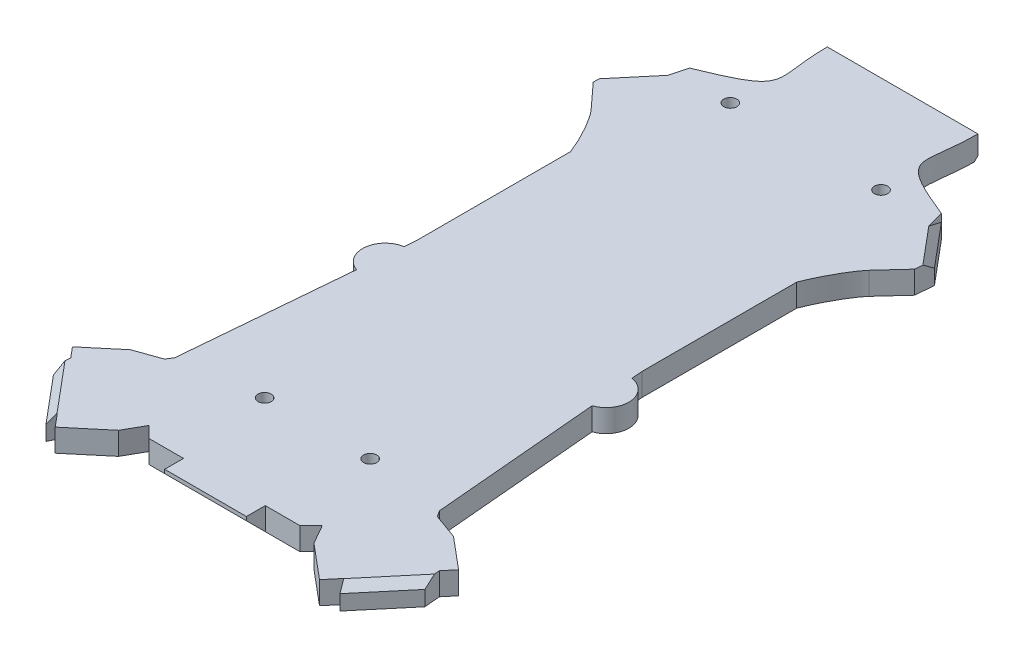
SolidWorks part; units mm, degrees
ref_plane "Front Plane" through (0, 0, 0) normal (0, 0, 1) x (1, 0, 0)
ref_plane "Top Plane" through (0, 0, 0) normal (0, 1, 0) x (1, 0, 0)
ref_plane "Right Plane" through (0, 0, 0) normal (1, 0, 0) x (0, 0, -1)
sketch "Sketch1" plane through (0, 0, 0) normal (0, 1, 0) x (1, 0, 0)
  line L1 (30, -90) -> (-30, -90)
  line L2 (30, -90) -> (30, 90)
  line L3 (30, 90) -> (-30, 90)
  line L4 (-30, -90) -> (-30, 90)
  line L5 (30, -90) -> (-30, 90) construction
  line L6 (30, 90) -> (-30, -90) construction
  point P0 (0, 0)
  dimension "D1" = 60
  dimension "D2" = 180
extrude "Boss-Extrude1" add sketch "Sketch1" along normal blind 6
sketch "Sketch2" plane through (0, 6, 0) normal (0, 1, 0) x (1, 0, 0)
  line L0 (0, -90) -> (0, -59.8277)
  line L1 (-30, -90) -> (30, -90) construction
sketch "Sketch3" plane through (0, 6, 0) normal (0, 1, 0) x (1, 0, 0)
  line L0 (-30, -90) -> (30, -90) construction
  line L1 (15.25, -33.25) -> (-15.25, -33.25)
  line L2 (15.25, -33.25) -> (15.25, -2.75)
  line L3 (15.25, -2.75) -> (-15.25, -2.75)
  line L4 (-15.25, -33.25) -> (-15.25, -2.75)
  line L5 (15.25, -33.25) -> (-15.25, -2.75) construction
  line L6 (15.25, -2.75) -> (-15.25, -33.25) construction
  line L7 (0, -18) -> (0, -90) construction
  point P0 (0, -18)
  dimension "D1" = 30.5
  dimension "D2" = 72
chamfer "Chamfer2" distance 10 angle 45 4 edges at (30, 3, -90) (-30, 3, -90) (-30, 3, 90) (30, 3, 90)
sketch "Sketch52" plane through (0, 6, 0) normal (0, 1, 0) x (1, 0, 0)
  line L0 (0, 28.8816) -> (0, 18.7178) construction
  line L1 (13.2149, 49.8944) -> (24.7851, 36.1056) construction
  line L2 (19, 43) -> (9.9357, 35.3941) construction
  line L4 (30, -80) -> (30, 80) construction
  line L7 (45, 53.0679) -> (36.85, 44.1738)
  line L8 (36.85, 44.1738) -> (30, 25.3535)
  line L10 (30, 79.657) -> (30, 25.3535)
  line L16 (33.4298, 66.8567) -> (45, 53.0679)
  line L17 (-33.4298, 66.8567) -> (-45, 53.0679)
  line L18 (-30, 79.657) -> (-33.4298, 66.8567)
  line L19 (-30, 79.657) -> (-30, 25.3535)
  line L20 (-36.85, 44.1738) -> (-30, 25.3535)
  line L21 (-45, 53.0679) -> (-36.85, 44.1738)
  line L22 (33.4298, 66.8567) -> (30, 79.657)
  line L23 (30, -80) -> (30, 80) construction
  point P25 (39.2149, 59.9623)
  dimension "D1" = 18
  dimension "D2" = 20
  dimension "D3" = 15
  dimension "D4" = 6.85
  dimension "D5" = 15
  dimension "D6" = 97.5
extrude "Boss-Extrude3" add sketch "Sketch52" against normal through all
sketch "Sketch53" plane through (0, 6, 0) normal (0, 1, 0) x (1, 0, 0)
  line L0 (25.7851, -63.1056) -> (14.2149, -76.8944) construction
  line L1 (20, -70) -> (7.555, -59.5574) construction
  line L3 (30, -80) -> (30, 25.3535) construction
  line L5 (30, -65.9896) -> (30, -80)
  line L7 (39, -98.3443) -> (51.213, -83.7894)
  line L8 (51.213, -83.7894) -> (30, -65.9896)
  line L9 (0, -71.0769) -> (0, -64.6229) construction
  line L10 (-51.213, -83.7894) -> (-30, -65.9896)
  line L11 (-39, -98.3443) -> (-51.213, -83.7894)
  line L12 (-30, -80) -> (-39, -98.3443)
  line L13 (-30, -65.9896) -> (-30, -80)
  line L14 (39, -98.3443) -> (30, -80)
  point P13 (45.1065, -91.0668)
  dimension "D1" = 9
  dimension "D2" = 19
extrude "Boss-Extrude4" add sketch "Sketch53" against normal through all
chamfer "Chamfer14" distance 2 angle 45 2 edges at (-45.1065, 6, 91.0668) (45.1065, 6, 91.0668)
chamfer "Chamfer16" distance 7 angle 45 2 edges at (30, 3, 65.9896) (-30, 3, 65.9896)
chamfer "Chamfer17" distance 2 angle 45 2 edges at (-39.2149, 6, -59.9623) (39.2149, 6, -59.9623)
sketch "Sketch59" plane through (0, 6, 0) normal (0, 1, 0) x (1, 0, 0)
  line L1 (-10.85, -90) -> (10.85, -90)
  line L2 (-10.85, -90) -> (-10.85, -95)
  line L3 (-10.85, -95) -> (10.85, -95)
  line L4 (10.85, -90) -> (10.85, -95)
  dimension "D1" = 5
extrude "Boss-Extrude5" add sketch "Sketch59" against normal through all
chamfer "Chamfer19" distance 5 angle 45 1 edges at (0, 0, 95)
sketch "Sketch61" plane through (0, 0, 0) normal (0, -1, 0) x (1, 0, 0)
  line L0 (30, -79.657) -> (20, -90)
  line L3 (20, -90) -> (30, -80)
  line L4 (30, -80) -> (30, -79.657)
  line L5 (0, -69.8334) -> (0, -62.3475) construction
  line L6 (-30, -80) -> (-30, -79.657)
  line L7 (-20, -90) -> (-30, -80)
  line L8 (-30, -79.657) -> (-20, -90)
extrude "Cut-Extrude28" cut sketch "Sketch61" against normal through all
chamfer "Chamfer20" distance 3 angle 45 4 edges at (-45, 2, -53.0679) (45, 2, -53.0679) (-51.213, 2, 83.7894) (51.213, 2, 83.7894)
sketch "Sketch62" plane through (0, 6, 0) normal (0, 1, 0) x (1, 0, 0)
  line L0 (0, 67.8456) -> (0, 57.6028) construction
  line L1 (34.6547, 62.2856) -> (30, 79.657) construction
  line L2 (33.4298, 66.8567) -> (43.0716, 55.3661) construction
  line L4 (20, 90) -> (30, 79.657)
  line L5 (30, 79.657) -> (33.4298, 66.8567)
  line L6 (20, 90) -> (33.4298, 66.8567) construction
  line L7 (26.7149, 78.4284) -> (24.1201, 76.9226) construction
  line L8 (-30, 79.657) -> (-33.4298, 66.8567)
  line L9 (-20, 90) -> (-30, 79.657)
  line L10 (20, 90) -> (-20, 90) construction
  spline S0 degree 3 poles (33.4298, 66.8567) (13.8497, 74.8047) (20, 74.5738) (20, 90) knots 0 0 0 0 1 1 1 1
  spline S1 degree 3 poles (-33.4298, 66.8567) (-13.8497, 74.8047) (-20, 74.5738) (-20, 90) knots 0 0 0 0 1 1 1 1
  dimension "D1" = 3
extrude "Cut-Extrude29" cut sketch "Sketch62" against normal through all
chamfer "Chamfer24" distance 1 angle 45 1 edges at (0, 0, -90)
sketch "Sketch64" plane through (0, 6, 0) normal (0, 1, 0) x (1, 0, 0)
  line L1 (36.85, 44.1738) -> (42.6458, 50.4988) construction
  line L4 (33.425, 34.7637) -> (31.5456, 35.4477) construction
  line L5 (30, 25.3535) -> (36.85, 44.1738) construction
  line L6 (36.85, 44.1738) -> (25, 5.3535)
  line L7 (0, 11.3453) -> (0, 14.5667) construction
  line L8 (-33.425, 34.7637) -> (-31.5456, 35.4477) construction
  line L9 (-36.85, 44.1738) -> (-25, 5.3535)
  spline S0 degree 3 poles (25, 5.3535) (25, 11.8885) (26.6752, 28.4247) (35.4951, 42.6951) (36.85, 44.1738) knots 0 0 0 0 0.75099 1 1 1 1
  spline S1 degree 3 poles (-25, 5.3535) (-25, 11.8885) (-26.6752, 28.4247) (-35.4951, 42.6951) (-36.85, 44.1738) knots 0 0 0 0 0.75099 1 1 1 1
  dimension "D1" = 2
extrude "Cut-Extrude31" cut sketch "Sketch64" against normal through all
sketch "Sketch66" plane through (0, 6, 0) normal (0, 1, 0) x (1, 0, 0)
  line L0 (29.3209, 35.8558) -> (29.3209, -18) construction
  line L1 (15.25, -2.75) -> (15.25, -33.25) construction
  line L7 (0, -18) -> (0, -26.2369) construction
  line L12 (15.25, -18) -> (29.3209, -18) construction
  line L13 (29.3209, -12) -> (25, -12)
  line L15 (25, -12) -> (25, -13.8371)
  line L16 (25, -24) -> (25, -22.1629)
  line L17 (29.3209, -24) -> (25, -24)
  line L18 (-29.3209, -24) -> (-25, -24)
  line L19 (-25, -24) -> (-25, -22.1629)
  line L20 (-25, -12) -> (-25, -13.8371)
  line L21 (-29.3209, -12) -> (-25, -12)
  circle A0 centre (29.3209, -18) radius 6
  circle A1 centre (-29.3209, -18) radius 6
  dimension "D1" = 12
extrude "Boss-Extrude6" add sketch "Sketch66" against normal blind 6 contours A0 | A0 L13 L15 | A0 L16 L17 | A1 | L21 A1 L20 | L19 A1 L18
sketch "Sketch67" plane through (0, 0, 0) normal (0, -1, 0) x (1, 0, 0)
  line L0 (30, -21.7334) -> (30, -31.8788)
  line L1 (-30, -21.7334) -> (-30, -31.8788)
  line L2 (25, -5.3535) -> (30, -21.7334) construction
  line L3 (-30, -21.7334) -> (-25, -5.3535) construction
  line L4 (25, -5.3535) -> (30, -21.7334)
  line L5 (-30, -21.7334) -> (-25, -5.3535)
  spline S0 degree 3 poles (-975.6534, 1680.3084) (107.6454, -94.0467) (-77.2559, -23.1232) (149.563, 178.3722) (-408.1539, -1957.0806) knots -2.174695 -2.174695 -2.174695 -2.174695 0.24901 5.416501 5.416501 5.416501 5.416501 only from (36.85, -44.1738) to (25, -5.3535) construction
  spline S1 degree 3 poles (408.1525, -1957.0752) (-149.5627, 178.3719) (77.2558, -23.1232) (-107.6453, -94.0467) (975.6526, 1680.3071) knots -4.416496 -4.416496 -4.416496 -4.416496 0.75099 3.174694 3.174694 3.174694 3.174694 only from (-25, -5.3535) to (-36.85, -44.1738) construction
  spline S2 degree 3 poles (30, -31.8788) (26.006, -21.7463) (25, -11.1974) (25, -5.3535) knots 0.32843 0.32843 0.32843 0.32843 1 1 1 1
  spline S3 degree 3 poles (-25, -5.3535) (-25, -11.1974) (-26.006, -21.7463) (-30, -31.8788) knots 0 0 0 0 0.67157 0.67157 0.67157 0.67157
extrude "Boss-Extrude7" add sketch "Sketch67" against normal up to surface (6 mm away) up to face at (-0.0523, 6, 17.7878)
sketch "Sketch70" plane through (0, 6, 0) normal (0, 1, 0) x (1, 0, 0)
  line L0 (-35.152, -68.0857) -> (-36.2077, -69.6952)
  line L2 (-36.2077, -69.6952) -> (-42.8678, -72.0706)
  line L4 (-48.9148, -81.8611) -> (-51.2372, -79.0933)
  line L6 (-51.2372, -79.0933) -> (-42.8678, -72.0706)
  line L9 (-37.956, -96.3808) -> (-29.9193, -80)
  line L10 (-35.3623, -70.4891) -> (-48.9148, -81.8611)
  line L11 (-22.967, -86.9523) -> (-25.9294, -92.1608)
  line L14 (0, -95) -> (0, -58.2577) construction
  line L15 (-37.956, -96.3808) -> (-35.0648, -99.8264)
  line L17 (-35.0648, -99.8264) -> (-25.9294, -92.1608)
  line L18 (-10.85, -95) -> (10.85, -95) construction
  line L19 (-35.3623, -70.4891) -> (-35.152, -68.0857)
  line L20 (-29.9193, -80) -> (-22.967, -86.9523)
  line L21 (35.3623, -70.4891) -> (48.9148, -81.8611)
  line L22 (48.9148, -81.8611) -> (51.2372, -79.0933)
  line L23 (51.2372, -79.0933) -> (42.8678, -72.0706)
  line L24 (36.2077, -69.6952) -> (42.8678, -72.0706)
  line L25 (35.152, -68.0857) -> (36.2077, -69.6952)
  line L26 (35.3623, -70.4891) -> (35.152, -68.0857)
  line L27 (37.956, -96.3808) -> (29.9193, -80)
  line L28 (37.956, -96.3808) -> (35.0648, -99.8264)
  line L29 (35.0648, -99.8264) -> (25.9294, -92.1608)
  line L30 (22.967, -86.9523) -> (25.9294, -92.1608)
  line L31 (29.9193, -80) -> (22.967, -86.9523)
extrude "Boss-Extrude8" add sketch "Sketch70" against normal up to surface (6 mm away) up to face at (-0.2064, 0, 18.9495)
sketch "Sketch71" plane through (0, 6, 0) normal (0, 1, 0) x (1, 0, 0)
  line L3 (-38.0367, -96.3808) -> (-37.956, -96.3808)
  line L4 (-30, -80) -> (-29.9459, -80.0541) construction
  line L5 (-38.0367, -96.3808) -> (-30, -80) construction
  line L6 (-29.9459, -80.0541) -> (-37.956, -96.3808) construction
  line L7 (-30, -80) -> (-29.9459, -80.0541)
  line L8 (-38.0367, -96.3808) -> (-30, -80)
  line L9 (-29.9459, -80.0541) -> (-37.956, -96.3808)
  line L10 (0, -95) -> (0, -75.7562) construction
  line L11 (-10.85, -95) -> (10.85, -95) construction
  line L12 (29.9459, -80.0541) -> (37.956, -96.3808)
  line L13 (38.0367, -96.3808) -> (30, -80)
  line L14 (30, -80) -> (29.9459, -80.0541)
  line L15 (38.0367, -96.3808) -> (37.956, -96.3808)
extrude "Boss-Extrude9" add sketch "Sketch71" against normal up to surface (6 mm away) up to face at (-0.1376, 0, 40.7114)
hole_wizard "Ø3.0mm Dowel Hole3" positions "Sketch74" profile "Sketch75" hole size "Ø3.0" standard "ANSI Metric" end condition through all
sketch "Sketch74" plane through (0, 6, 0) normal (0, 1, 0) x (1, 0, 0)
  line L0 (0, 90) -> (0, -95) construction
  line L1 (20, 90) -> (-20, 90) construction
  line L2 (-10.85, -95) -> (10.85, -95) construction
  line L4 (-20, 64.2603) -> (20, 64.2603) construction
  line L6 (-14, -65.3215) -> (14, -65.3215) construction
  point P0 (20, 64.2603)
  point P2 (-20, 64.2603)
  point P4 (-14, -65.3215)
  point P6 (14, -65.3215)
  dimension "D1" = 40
  dimension "D2" = 20
  dimension "D3" = 28
  dimension "D4" = 14
sketch "Sketch75" plane through (20, 6, -64.2603) normal (1, 0, 0) x (0, 0, 1)
  line L0 (0, 0) -> (0, 6)
  line L1 (0, 6) -> (1.75, 6)
  line L2 (1.75, 6) -> (1.75, 0)
  line L5 (1.75, 0) -> (0, 0)
  line L11 (0, -6.35) -> (0, 107.95) construction
  dimension "Thru Hole Dia." = 3.5
  dimension "Thru Hole Depth" = 6
